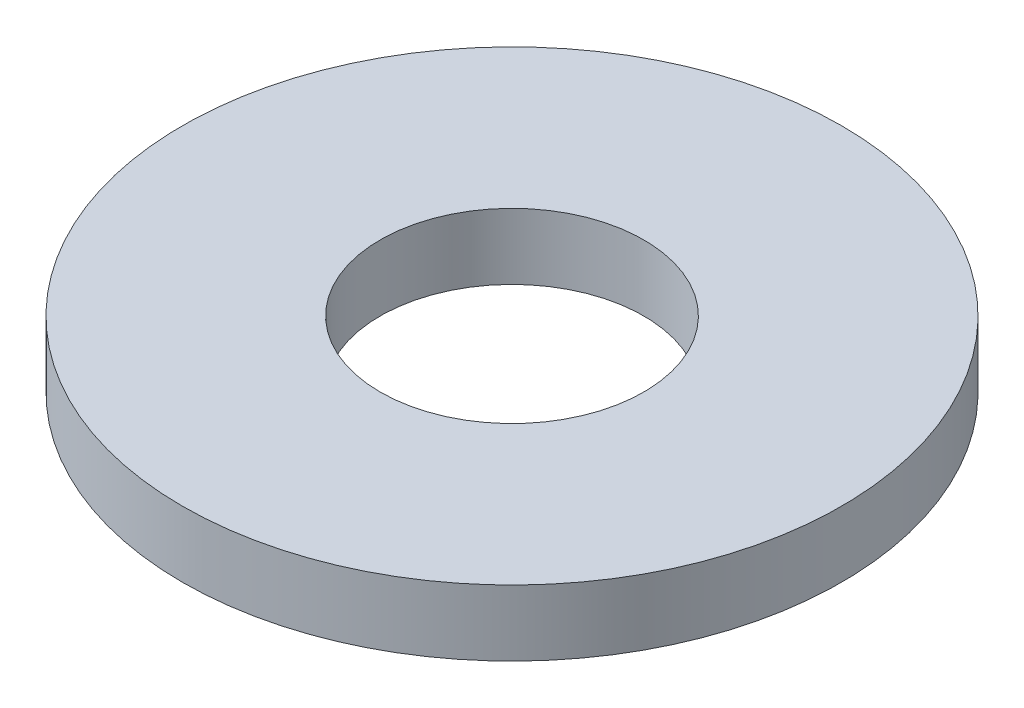
SolidWorks part; units mm, degrees
material "AISI 304"
ref_plane "前视基准面" through (0, 0, 0) normal (0, 0, 1) x (1, 0, 0)
ref_plane "上视基准面" through (0, 0, 0) normal (0, 1, 0) x (1, 0, 0)
ref_plane "右视基准面" through (0, 0, 0) normal (1, 0, 0) x (0, 0, -1)
sketch "草图1" plane through (0, 0, 0) normal (0, 1, 0) x (1, 0, 0)
  circle A0 centre (0, 0) radius 1
  circle A1 centre (0, 0) radius 2.5
  dimension "D1" = 2
  dimension "D2" = 5
extrude "凸台-拉伸1" add sketch "草图1" along normal blind 0.5
